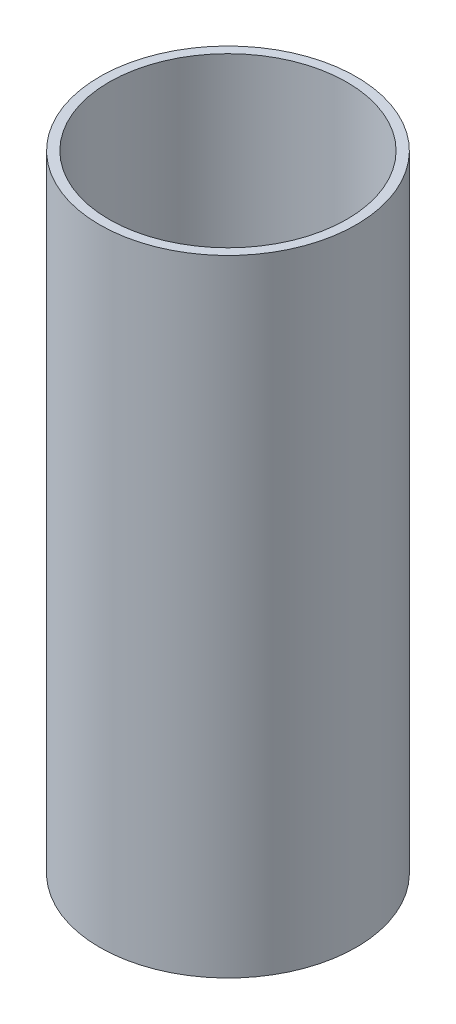
SolidWorks part; units mm, degrees
ref_plane "Front Plane" through (0, 0, 0) normal (0, 0, 1) x (1, 0, 0)
ref_plane "Top Plane" through (0, 0, 0) normal (0, 1, 0) x (1, 0, 0)
ref_plane "Right Plane" through (0, 0, 0) normal (1, 0, 0) x (0, 0, -1)
sketch "Sketch1" plane through (0, 0, 0) normal (0, 1, 0) x (1, 0, 0)
  circle A0 centre (0, 0) radius 19
  circle A1 centre (0, 0) radius 20.5
  dimension "D1" = 38
  dimension "D2" = 41
extrude "Boss-Extrude1" add sketch "Sketch1" along normal blind 100
